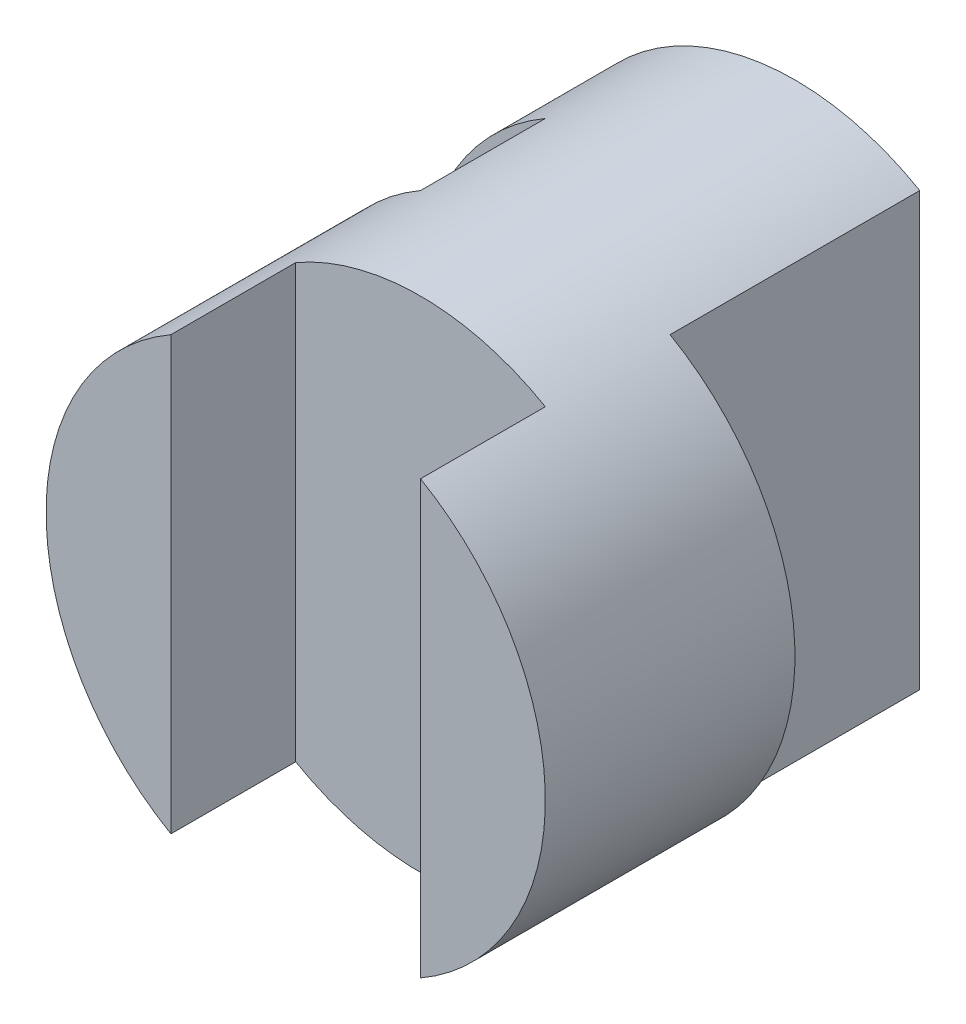
SolidWorks part; units mm, degrees
ref_plane "Front" through (0, 0, 0) normal (0, 0, 1) x (1, 0, 0)
ref_plane "Top" through (0, 0, 0) normal (0, 1, 0) x (1, 0, 0)
ref_plane "Right" through (0, 0, 0) normal (1, 0, 0) x (0, 0, -1)
sketch "Sketch1" plane through (0, 0, 0) normal (0, 0, 1) x (1, 0, 0)
  circle A0 centre (0, 0) radius 2
  dimension "D1" = 4
extrude "Boss-Extrude1" add sketch "Sketch1" along normal blind 4
sketch "Sketch2" plane through (0, 0, 0) normal (0, 1, 0) x (1, 0, 0)
  line L0 (-2, 0) -> (-2, -4) construction
  line L1 (-2, -1) -> (-1, -1)
  line L2 (-2, -1) -> (-2, -2)
  line L3 (-2, -2) -> (-1, -2)
  line L4 (-1, -1) -> (-1, -2)
  line L5 (2, 0) -> (-2, 0) construction
  line L6 (-2, -4) -> (2, -4) construction
  line L7 (2, 0) -> (1, 0)
  line L8 (2, 0) -> (2, -2)
  line L9 (2, -2) -> (1, -2)
  line L10 (1, 0) -> (1, -2)
  line L11 (-1, -4) -> (1, -4)
  line L12 (-1, -4) -> (-1, -3)
  line L13 (-1, -3) -> (1, -3)
  line L14 (1, -4) -> (1, -3)
  dimension "D1" = 0
  dimension "D2" = 1
  dimension "D3" = 1
  dimension "D4" = 1
  dimension "D5" = 1
  dimension "D6" = 2
  dimension "D7" = 2
  dimension "D8" = 1
  dimension "D9" = 1
extrude "Cut-Extrude1" cut sketch "Sketch2" against normal mid plane 10
